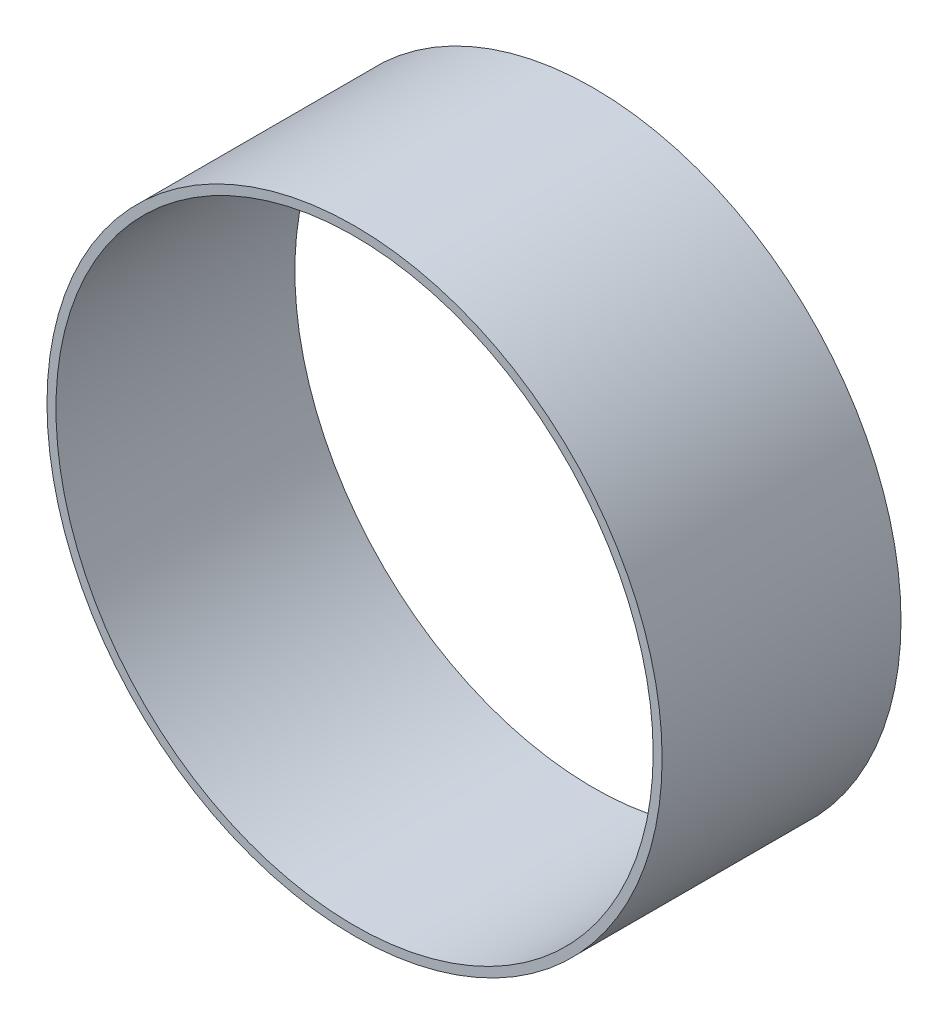
SolidWorks part; units mm, degrees
ref_plane "Front Plane" through (0, 0, 0) normal (0, 0, 1) x (1, 0, 0)
ref_plane "Top Plane" through (0, 0, 0) normal (0, 1, 0) x (1, 0, 0)
ref_plane "Right Plane" through (0, 0, 0) normal (1, 0, 0) x (0, 0, -1)
sketch "Sketch1" plane through (0, 0, 0) normal (0, 0, 1) x (1, 0, 0)
  circle A0 centre (0, 0) radius 65.405
  circle A1 centre (0, 0) radius 63.5
  dimension "D1" = 127
  dimension "D2" = 130.81
extrude "Boss-Extrude1" add sketch "Sketch1" along normal mid plane 50.8
equation "\"AIRFRAME_OD\"= 5.15in"
equation "\"AIRFRAME_ID\"= 5.00in"
equation "\"FLAT_T\"= 0.125in"
equation "\"NOSE_EXP_L\"= 27in"
equation "\"NOSE_SHOULDER_L\"= 5in"
equation "\"MAIN_L\"= 30in"
equation "\"RECO_COUP_L\"= 10in"
equation "\"RECO_SWITCH_L\"= 2in"
equation "\"DROGUE_L\"= 20in"
equation "\"ATS_FORE_COUP_L\"= 5.5in"
equation "\"ATS_AFT_COUP_L\"= 4.5in"
equation "\"LOWER_L\"= 30in"
equation "\"FIN_N\"= 4"
equation "\"CR_AFT_X\"= 0.5in"
equation "\"CR_FORE_X\"= 9.25in"
equation "\"D1@Sketch1\"=\"AIRFRAME_ID\""
equation "\"D2@Sketch1\"=\"AIRFRAME_OD\""
equation "\"D1@Boss-Extrude1\"=\"RECO_SWITCH_L\""
equation "\"FIN_ROOT\"= 8in"
equation "\"FIN_X\"= 0.75in"
equation "\"MOTOR_OD\"= 3.091in"
equation "\"MOTOR_ID\"= 3.00in"
equation "\"COUPLER_OD\"= 4.998in"
equation "\"COUPLER_ID\"= 4.88in"
equation "\"RECO_ROD_X\"= 3.5in"
equation "\"ATS_ROD_X\"= 3in"
equation "\"MOTOR_L\"= 14in"
equation "\"MOTOR_LOWER_X\"= 2in"
